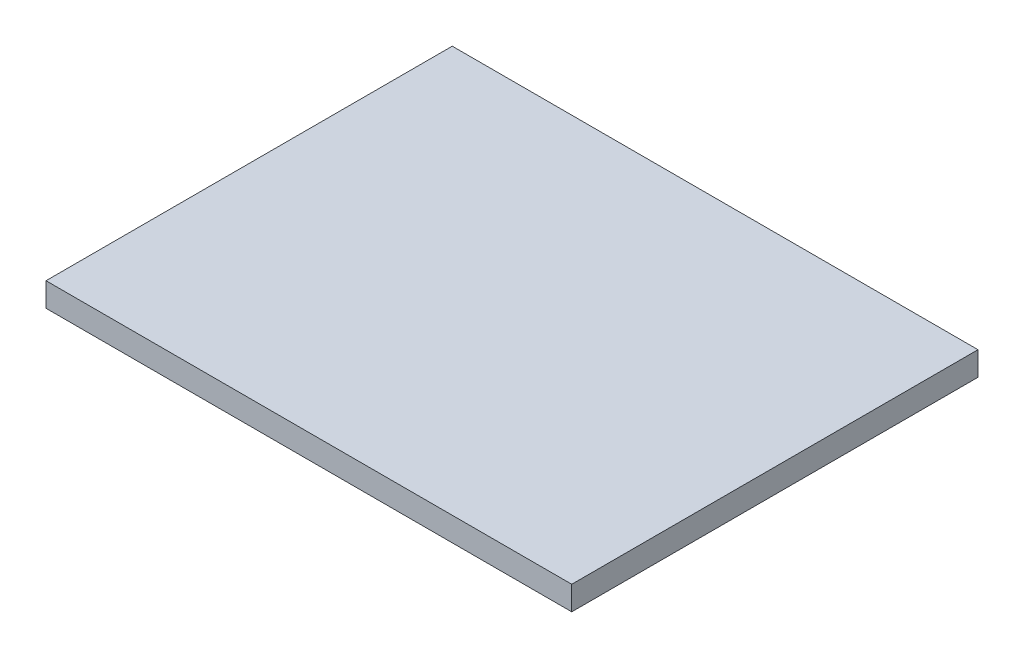
SolidWorks part; units mm, degrees
ref_plane "前视基准面" through (0, 0, 0) normal (0, 0, 1) x (1, 0, 0)
ref_plane "上视基准面" through (0, 0, 0) normal (0, 1, 0) x (1, 0, 0)
ref_plane "右视基准面" through (0, 0, 0) normal (1, 0, 0) x (0, 0, -1)
sketch "草图1" plane through (0, 0, 0) normal (0, 1, 0) x (1, 0, 0)
  line L1 (-22, -17) -> (22, -17)
  line L2 (-22, -17) -> (-22, 17)
  line L3 (-22, 17) -> (22, 17)
  line L4 (22, -17) -> (22, 17)
  line L5 (-22, -17) -> (22, 17) construction
  line L6 (-22, 17) -> (22, -17) construction
  point P0 (0, 0)
extrude "凸台-拉伸1" add sketch "草图1" along normal blind 2
